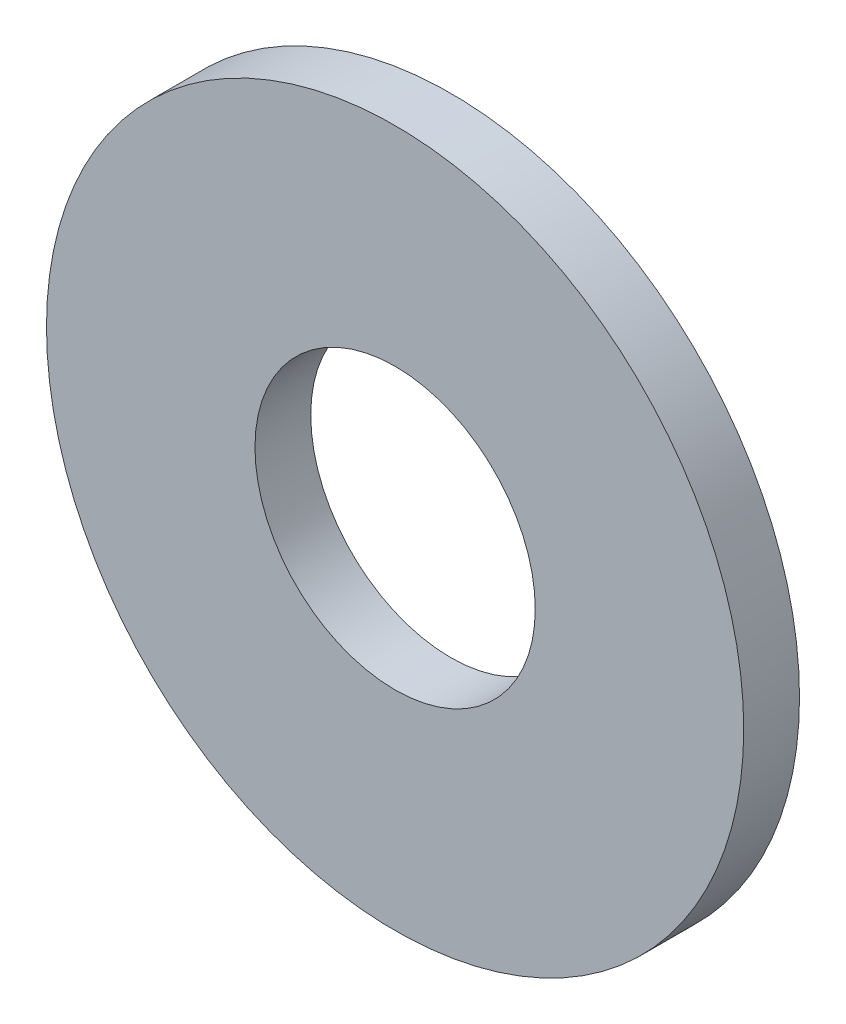
SolidWorks part; units mm, degrees
material "Plain Carbon Steel"
ref_plane "Front Plane" through (0, 0, 0) normal (0, 0, 1) x (1, 0, 0)
ref_plane "Top Plane" through (0, 0, 0) normal (0, 1, 0) x (1, 0, 0)
ref_plane "Right Plane" through (0, 0, 0) normal (1, 0, 0) x (0, 0, -1)
sketch "Sketch1" plane through (0, 0, 0) normal (0, 0, 1) x (1, 0, 0)
  circle A0 centre (0, 0) radius 2.5527
  circle A1 centre (0, 0) radius 6.35
  dimension "D1" = 12.7
  dimension "D2" = 5.1054
extrude "Boss-Extrude1" add sketch "Sketch1" along normal blind 1.016
